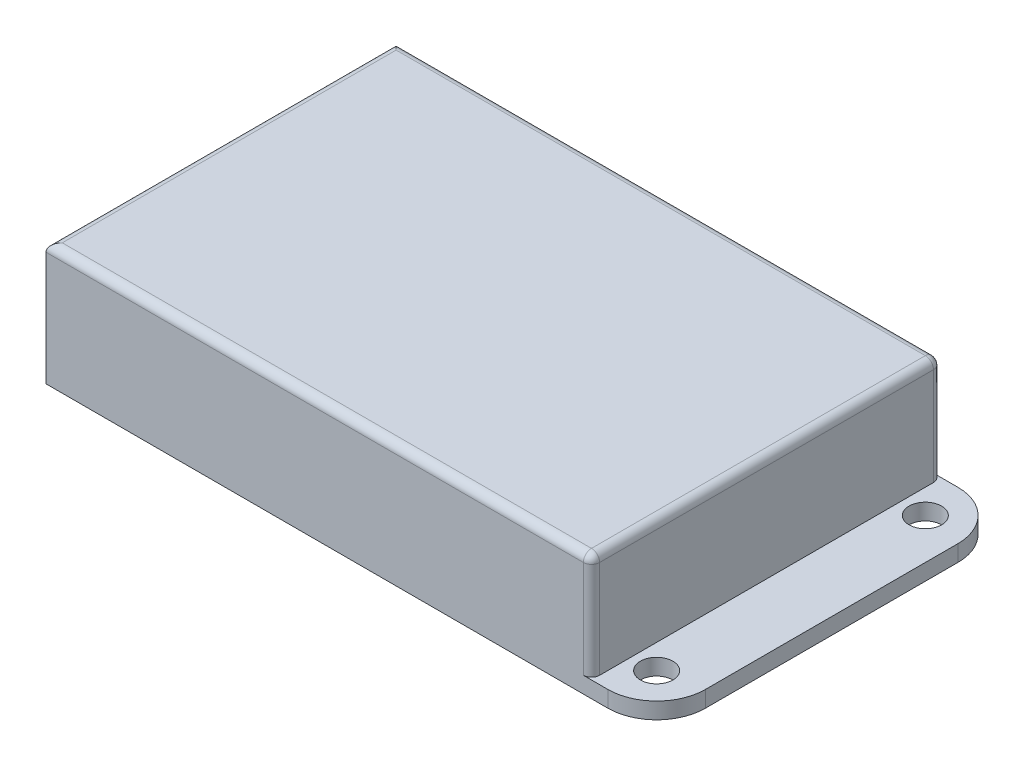
SolidWorks part; units mm, degrees
ref_plane "前视基准面" through (0, 0, 0) normal (0, 0, 1) x (1, 0, 0)
ref_plane "上视基准面" through (0, 0, 0) normal (0, 1, 0) x (1, 0, 0)
ref_plane "右视基准面" through (0, 0, 0) normal (1, 0, 0) x (0, 0, -1)
other "Configuration Table"
sketch "Sketch1" plane through (0, 0, 0) normal (0, 1, 0) x (1, 0, 0)
  line L1 (0, 0) -> (85, 0)
  line L2 (0, 0) -> (0, -43)
  line L3 (0, -43) -> (85, -43)
  line L4 (85, 0) -> (85, -43)
  spline S0 degree 2 poles (10, 0) (-10, -21.5) (10, -43) knots 0 0 0 1 1 1
  point P7 (0, 0)
  point P9 (0, -21.5)
  point P10 (0, 0)
  dimension "D1" = 43
  dimension "D2" = 85
  dimension "D3" = 10
extrude "Boss-Extrude1" add sketch "Sketch1" along normal blind 2 contours L1 S0 L3 L4
sketch "Sketch2" plane through (0, 2, 0) normal (0, 1, 0) x (1, 0, 0)
  line L0 (10, 0) -> (85, 0) construction
  line L1 (10, 0) -> (77, 0)
  line L2 (10, 0) -> (10, -43)
  line L3 (10, -43) -> (77, -43)
  line L4 (77, 0) -> (77, -43)
  line L5 (10, -43) -> (85, -43) construction
  line L6 (85, 0) -> (85, -43) construction
  point P10 (0, 0)
  point P12 (0, 0)
  dimension "D1" = 8
extrude "Boss-Extrude2" add sketch "Sketch2" along normal blind 13
sketch "Sketch3" plane through (0, 2, 0) normal (0, 1, 0) x (1, 0, 0)
  line L0 (85, 0) -> (85, -43) construction
  line L1 (77, -43) -> (85, -43) construction
  circle A0 centre (80, -5) radius 2
  circle A1 centre (80, -38) radius 2
  circle A2 centre (5, -21.5) radius 2
  point P8 (0, 0)
  point P11 (0, 0)
  dimension "D3" = 4
  dimension "D4" = 4
  dimension "D6" = 4
  dimension "D1" = 5
  dimension "D2" = 5
  dimension "D5" = 33
  dimension "D7" = 75
  dimension "D8" = 16.5
extrude "Cut-Extrude1" cut sketch "Sketch3" against normal through all
fillet "Fillet1" radius 6 2 edges at (85, 1, 0) (85, 1, 43)
fillet "Fillet2" radius 1 6 edges at (43.5, 15, 0) (77, 15, 21.5) (43.5, 15, 43) (10, 15, 21.5) (77, 8.5, 0) (77, 8.5, 43)
